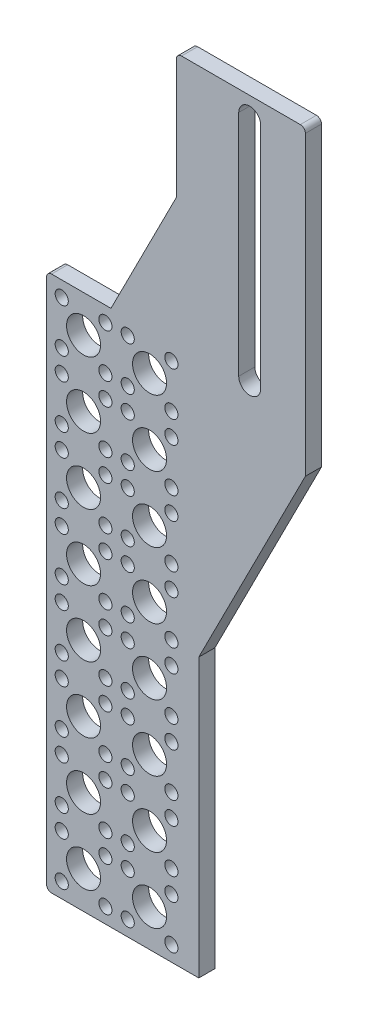
SolidWorks part; units mm, degrees
ref_plane "Front Plane" through (0, 0, 0) normal (0, 0, 1) x (1, 0, 0)
ref_plane "Top Plane" through (0, 0, 0) normal (0, 1, 0) x (1, 0, 0)
ref_plane "Right Plane" through (0, 0, 0) normal (1, 0, 0) x (0, 0, -1)
sketch "Reference Sketch" plane through (0, 0, 0) normal (0, 0, 1) x (1, 0, 0)
  line L0 (0, 0) -> (0, 25.019) construction
  line L1 (35.019, 0) -> (35.019, -50.019) construction
  line L2 (-1.725, 25.019) -> (1.725, 25.019)
  line L6 (35.019, -50.019) -> (-35.019, -50.019) construction
  line L7 (-35.019, 0) -> (-112.4213, 0) construction
  line L8 (-35.019, -50.019) -> (-35.019, 0) construction
  line L9 (0, -35.019) -> (0, -50.019) construction
  line L10 (-35.019, -50.019) -> (-75, -50.019)
  line L11 (35.019, 0) -> (112.4213, 0) construction
  line L12 (-75, -50.019) -> (-75, -120.019)
  line L13 (-75, -120.019) -> (75, -120.019)
  line L14 (75, -120.019) -> (75, -50.019)
  line L15 (35.019, -50.019) -> (75, -50.019)
  line L16 (0, 35.019) -> (70, 35.019)
  line L17 (70, 35.019) -> (70, -35.019)
  line L19 (0, 35.019) -> (-70, 35.019)
  line L20 (-70, 35.019) -> (-70, -35.019)
  line L22 (-35, -35.019) -> (-35.019, -50.019)
  line L23 (-128.24, -30) -> (-108.24, -30) construction
  line L24 (-128.24, -30) -> (-128.24, -140) construction
  line L25 (-128.24, -140) -> (-108.24, -140) construction
  line L26 (-108.24, -30) -> (-108.24, -140) construction
  line L27 (35.019, -50.019) -> (35, -35.019)
  line L28 (70, -35.019) -> (35, -35.019)
  line L29 (-50, -55.019) -> (50, -55.019) construction
  line L30 (-50, -55.019) -> (-50, -115.019) construction
  line L31 (-50, -115.019) -> (50, -115.019) construction
  line L32 (50, -55.019) -> (50, -115.019) construction
  line L33 (-35, -35.019) -> (-70, -35.019)
  circle A0 centre (0, 0) radius 25.019 construction
  circle A1 centre (0, 25.019) radius 1.725 construction
  circle A2 centre (17.6911, 17.6911) radius 1.725 construction
  circle A3 centre (25.019, 0) radius 1.725 construction
  circle A4 centre (17.6911, -17.6911) radius 1.725 construction
  circle A5 centre (0, -25.019) radius 1.725 construction
  circle A6 centre (-17.6911, -17.6911) radius 1.725 construction
  circle A7 centre (0, -82.931) radius 139.7 construction
  circle A8 centre (0, -82.931) radius 13.9065 construction
  circle A9 centre (0, 0) radius 35.019 construction
  circle A10 centre (-25.019, 0) radius 1.725 construction
  circle A11 centre (-17.6911, 17.6911) radius 1.725 construction
  circle A12 centre (0, 0) radius 2.16 construction
  circle A13 centre (-63.2127, 5.019) radius 2.16
  circle A14 centre (-63.2127, 5.019) radius 2.8702 construction
  circle A15 centre (-53.2127, 5.019) radius 2.16
  circle A16 centre (-53.2127, 5.019) radius 2.8702 construction
  circle A17 centre (-53.2127, -4.981) radius 2.16
  circle A18 centre (-53.2127, -4.981) radius 2.8702 construction
  circle A19 centre (-53.2127, -14.981) radius 2.16
  circle A20 centre (-53.2127, -14.981) radius 2.8702 construction
  circle A21 centre (-53.2127, -24.981) radius 2.16
  circle A22 centre (-53.2127, -24.981) radius 2.8702 construction
  circle A23 centre (-63.2127, -4.981) radius 2.16
  circle A24 centre (-63.2127, -4.981) radius 2.8702 construction
  circle A25 centre (-63.2127, -14.981) radius 2.16
  circle A26 centre (-63.2127, -14.981) radius 2.8702 construction
  circle A27 centre (-63.2127, -24.981) radius 2.16
  circle A28 centre (-63.2127, -24.981) radius 2.8702 construction
  circle A29 centre (0, -82.931) radius 177.8 construction
  point P23 (0, 56.769)
  point P52 (0, -115.019)
  point P54 (50, -85.019)
  point P56 (75, -85.019)
  point P63 (35.0095, -42.519)
  point P64 (0, -42.519)
  dimension "D1" = 50.038
  dimension "D2" = 3.45
  dimension "D5" = 279.4
  dimension "D10" = 27.813
  dimension "D12" = 10
  dimension "D19" = 4.32
  dimension "D21" = 70.038
  dimension "D22" = 50.038
  dimension "D23" = 4.32
  dimension "D24" = 5.7404
  dimension "D31" = 355.6
  dimension "D4" = 25.019
  dimension "D6" = 31.75
  dimension "D7" = 15
  dimension "D8" = 70
  dimension "D9" = 108.24
  dimension "D11" = 30
  dimension "D13" = 20
  dimension "D14" = 110
  dimension "D15" = 150
  dimension "D16" = 70
  dimension "D17" = 100
  dimension "D18" = 60
  dimension "D20" = 35
  dimension "D27" = 10
  dimension "D28" = 10
  dimension "D29" = 30
  dimension "D30" = 6.7873
  dimension "D25" = 2
  dimension "D26" = 4
  dimension "D3" = 8
sketch "Sketch2" plane through (0, 0, 0) normal (0, 0, 1) x (1, 0, 0)
  line L0 (-116.64, -33.131) -> (-125.24, -33.131) construction
  line L2 (-128.24, -30.131) -> (-128.24, -135.731)
  line L3 (-128.24, -135.731) -> (-98.24, -135.731)
  line L5 (-125.24, -33.131) -> (-125.24, -41.731) construction
  line L6 (-77.24, -30.131) -> (-77.24, -39.631)
  line L8 (-102.64, -30.131) -> (-102.64, 19.869)
  line L9 (-102.64, 19.869) -> (-77.24, 19.869)
  line L10 (-77.24, -30.131) -> (-77.24, 19.869)
  line L11 (-88.2127, 15.869) -> (-88.2127, -29.131) construction
  line L12 (-86.0527, 15.869) -> (-86.0527, -29.131)
  line L13 (-90.3727, 15.869) -> (-90.3727, -29.131)
  line L14 (-128.24, -30.131) -> (-77.24, -30.131)
  line L15 (0, -82.931) -> (139.7, -82.931) construction
  line L16 (-128.24, -30) -> (-128.24, -140) construction
  line L17 (-102.64, -4.731) -> (-115.54, -30.131)
  line L20 (-77.24, -39.631) -> (-98.24, -80.9798)
  line L21 (-77.24, -39.631) -> (-128.24, -39.631) construction
  line L22 (-98.24, -80.9798) -> (-98.24, -135.731)
  line L23 (-101.59, -43.781) -> (-101.59, -31.081) construction
  line L24 (-114.59, -43.781) -> (-127.29, -43.781) construction
  line L25 (-114.59, -43.781) -> (-114.59, -31.081) construction
  line L26 (-114.59, -31.081) -> (-127.29, -31.081) construction
  line L27 (-127.29, -43.781) -> (-127.29, -31.081) construction
  line L28 (-101.59, -43.781) -> (-114.29, -43.781) construction
  line L29 (-101.59, -31.081) -> (-114.29, -31.081) construction
  line L30 (-114.29, -43.781) -> (-114.29, -31.081) construction
  line L31 (-101.59, -56.781) -> (-101.59, -44.081) construction
  line L32 (-101.59, -56.781) -> (-114.29, -56.781) construction
  line L33 (-101.59, -44.081) -> (-114.29, -44.081) construction
  line L34 (-114.29, -56.781) -> (-114.29, -44.081) construction
  line L35 (-101.59, -69.781) -> (-101.59, -57.081) construction
  line L36 (-101.59, -69.781) -> (-114.29, -69.781) construction
  line L37 (-101.59, -57.081) -> (-114.29, -57.081) construction
  line L38 (-114.29, -69.781) -> (-114.29, -57.081) construction
  line L39 (-101.59, -82.781) -> (-101.59, -70.081) construction
  line L40 (-101.59, -82.781) -> (-114.29, -82.781) construction
  line L41 (-101.59, -70.081) -> (-114.29, -70.081) construction
  line L42 (-114.29, -82.781) -> (-114.29, -70.081) construction
  line L43 (-101.59, -95.781) -> (-101.59, -83.081) construction
  line L44 (-101.59, -95.781) -> (-114.29, -95.781) construction
  line L45 (-101.59, -83.081) -> (-114.29, -83.081) construction
  line L46 (-114.29, -95.781) -> (-114.29, -83.081) construction
  line L47 (-101.59, -108.781) -> (-101.59, -96.081) construction
  line L48 (-101.59, -108.781) -> (-114.29, -108.781) construction
  line L49 (-101.59, -96.081) -> (-114.29, -96.081) construction
  line L50 (-114.29, -108.781) -> (-114.29, -96.081) construction
  line L51 (-101.59, -121.781) -> (-101.59, -109.081) construction
  line L52 (-101.59, -121.781) -> (-114.29, -121.781) construction
  line L53 (-101.59, -109.081) -> (-114.29, -109.081) construction
  line L54 (-114.29, -121.781) -> (-114.29, -109.081) construction
  line L55 (-101.59, -134.781) -> (-101.59, -122.081) construction
  line L56 (-101.59, -134.781) -> (-114.29, -134.781) construction
  line L57 (-101.59, -122.081) -> (-114.29, -122.081) construction
  line L58 (-114.29, -134.781) -> (-114.29, -122.081) construction
  line L59 (-114.59, -56.781) -> (-114.59, -44.081) construction
  line L60 (-114.59, -56.781) -> (-127.29, -56.781) construction
  line L61 (-114.59, -44.081) -> (-127.29, -44.081) construction
  line L62 (-127.29, -56.781) -> (-127.29, -44.081) construction
  line L63 (-114.59, -69.781) -> (-114.59, -57.081) construction
  line L64 (-114.59, -69.781) -> (-127.29, -69.781) construction
  line L65 (-114.59, -57.081) -> (-127.29, -57.081) construction
  line L66 (-127.29, -69.781) -> (-127.29, -57.081) construction
  line L67 (-114.59, -82.781) -> (-114.59, -70.081) construction
  line L68 (-114.59, -82.781) -> (-127.29, -82.781) construction
  line L69 (-114.59, -70.081) -> (-127.29, -70.081) construction
  line L70 (-127.29, -82.781) -> (-127.29, -70.081) construction
  line L71 (-114.59, -95.781) -> (-114.59, -83.081) construction
  line L72 (-114.59, -95.781) -> (-127.29, -95.781) construction
  line L73 (-114.59, -83.081) -> (-127.29, -83.081) construction
  line L74 (-127.29, -95.781) -> (-127.29, -83.081) construction
  line L75 (-114.59, -108.781) -> (-114.59, -96.081) construction
  line L76 (-114.59, -108.781) -> (-127.29, -108.781) construction
  line L77 (-114.59, -96.081) -> (-127.29, -96.081) construction
  line L78 (-127.29, -108.781) -> (-127.29, -96.081) construction
  line L79 (-114.59, -121.781) -> (-114.59, -109.081) construction
  line L80 (-114.59, -121.781) -> (-127.29, -121.781) construction
  line L81 (-114.59, -109.081) -> (-127.29, -109.081) construction
  line L82 (-127.29, -121.781) -> (-127.29, -109.081) construction
  line L83 (-114.59, -134.781) -> (-114.59, -122.081) construction
  line L84 (-114.59, -134.781) -> (-127.29, -134.781) construction
  line L85 (-114.59, -122.081) -> (-127.29, -122.081) construction
  line L86 (-127.29, -134.781) -> (-127.29, -122.081) construction
  circle A0 centre (-125.24, -33.131) radius 1.2954
  circle A1 centre (-125.24, -41.731) radius 1.2954
  circle A2 centre (-120.94, -37.431) radius 3.35
  circle A3 centre (-116.64, -33.131) radius 1.2954
  circle A4 centre (-116.64, -41.731) radius 1.2954
  arc A80 (-86.0527, 15.869) -> (-90.3727, 15.869) centre (-88.2127, 15.869) ccw
  arc A81 (-90.3727, -29.131) -> (-86.0527, -29.131) centre (-88.2127, -29.131) ccw
  circle A82 centre (0, -82.931) radius 139.7 construction
  circle A83 centre (-107.94, -37.431) radius 3.35
  circle A84 centre (-103.64, -33.131) radius 1.2954
  circle A85 centre (-112.24, -41.731) radius 1.2954
  circle A86 centre (-112.24, -33.131) radius 1.2954
  circle A87 centre (-103.64, -41.731) radius 1.2954
  circle A88 centre (-107.94, -50.431) radius 3.35
  circle A89 centre (-103.64, -46.131) radius 1.2954
  circle A90 centre (-112.24, -54.731) radius 1.2954
  circle A91 centre (-112.24, -46.131) radius 1.2954
  circle A92 centre (-103.64, -54.731) radius 1.2954
  circle A93 centre (-107.94, -63.431) radius 3.35
  circle A94 centre (-103.64, -59.131) radius 1.2954
  circle A95 centre (-112.24, -67.731) radius 1.2954
  circle A96 centre (-112.24, -59.131) radius 1.2954
  circle A97 centre (-103.64, -67.731) radius 1.2954
  circle A98 centre (-107.94, -76.431) radius 3.35
  circle A99 centre (-103.64, -72.131) radius 1.2954
  circle A100 centre (-112.24, -80.731) radius 1.2954
  circle A101 centre (-112.24, -72.131) radius 1.2954
  circle A102 centre (-103.64, -80.731) radius 1.2954
  circle A103 centre (-107.94, -89.431) radius 3.35
  circle A104 centre (-103.64, -85.131) radius 1.2954
  circle A105 centre (-112.24, -93.731) radius 1.2954
  circle A106 centre (-112.24, -85.131) radius 1.2954
  circle A107 centre (-103.64, -93.731) radius 1.2954
  circle A108 centre (-107.94, -102.431) radius 3.35
  circle A109 centre (-103.64, -98.131) radius 1.2954
  circle A110 centre (-112.24, -106.731) radius 1.2954
  circle A111 centre (-112.24, -98.131) radius 1.2954
  circle A112 centre (-103.64, -106.731) radius 1.2954
  circle A113 centre (-107.94, -115.431) radius 3.35
  circle A114 centre (-103.64, -111.131) radius 1.2954
  circle A115 centre (-112.24, -119.731) radius 1.2954
  circle A116 centre (-112.24, -111.131) radius 1.2954
  circle A117 centre (-103.64, -119.731) radius 1.2954
  circle A118 centre (-107.94, -128.431) radius 3.35
  circle A119 centre (-103.64, -124.131) radius 1.2954
  circle A120 centre (-112.24, -132.731) radius 1.2954
  circle A121 centre (-112.24, -124.131) radius 1.2954
  circle A122 centre (-103.64, -132.731) radius 1.2954
  circle A123 centre (-120.94, -50.431) radius 3.35
  circle A124 centre (-116.64, -46.131) radius 1.2954
  circle A125 centre (-125.24, -54.731) radius 1.2954
  circle A126 centre (-125.24, -46.131) radius 1.2954
  circle A127 centre (-116.64, -54.731) radius 1.2954
  circle A128 centre (-120.94, -63.431) radius 3.35
  circle A129 centre (-116.64, -59.131) radius 1.2954
  circle A130 centre (-125.24, -67.731) radius 1.2954
  circle A131 centre (-125.24, -59.131) radius 1.2954
  circle A132 centre (-116.64, -67.731) radius 1.2954
  circle A133 centre (-120.94, -76.431) radius 3.35
  circle A134 centre (-116.64, -72.131) radius 1.2954
  circle A135 centre (-125.24, -80.731) radius 1.2954
  circle A136 centre (-125.24, -72.131) radius 1.2954
  circle A137 centre (-116.64, -80.731) radius 1.2954
  circle A138 centre (-120.94, -89.431) radius 3.35
  circle A139 centre (-116.64, -85.131) radius 1.2954
  circle A140 centre (-125.24, -93.731) radius 1.2954
  circle A141 centre (-125.24, -85.131) radius 1.2954
  circle A142 centre (-116.64, -93.731) radius 1.2954
  circle A143 centre (-120.94, -102.431) radius 3.35
  circle A144 centre (-116.64, -98.131) radius 1.2954
  circle A145 centre (-125.24, -106.731) radius 1.2954
  circle A146 centre (-125.24, -98.131) radius 1.2954
  circle A147 centre (-116.64, -106.731) radius 1.2954
  circle A148 centre (-120.94, -115.431) radius 3.35
  circle A149 centre (-116.64, -111.131) radius 1.2954
  circle A150 centre (-125.24, -119.731) radius 1.2954
  circle A151 centre (-125.24, -111.131) radius 1.2954
  circle A152 centre (-116.64, -119.731) radius 1.2954
  circle A153 centre (-120.94, -128.431) radius 3.35
  circle A154 centre (-116.64, -124.131) radius 1.2954
  circle A155 centre (-125.24, -132.731) radius 1.2954
  circle A156 centre (-125.24, -124.131) radius 1.2954
  circle A157 centre (-116.64, -132.731) radius 1.2954
  point P14 (-120.94, -33.131)
  point P15 (-125.24, -37.431)
  point P17 (-88.2127, -6.631)
  point P21 (-120.94, -31.081)
  point P22 (-114.59, -37.431)
  point P23 (0, 0)
  point P24 (-128.19, -142.6712)
  point P195 (-128.24, -82.931)
  dimension "D1" = 2.5908
  dimension "D3" = 6.7
  dimension "D10" = 2.16
  dimension "D2" = 8.6
  dimension "D5" = 3
  dimension "D12" = 50
  dimension "D13" = 25.4
  dimension "D11" = 3
  dimension "D14" = 4
  dimension "D15" = 45
  dimension "D17" = 12.7
  dimension "D18" = 25.4
  dimension "D21" = 30
  dimension "D9" = 9.5
  dimension "D19" = 21
  dimension "D4" = 25
  dimension "D7" = 12.7
  dimension "D8" = 13
  dimension "D16" = 13
  dimension "D22" = 3
  dimension "D6" = 2
  dimension "D20" = 8
extrude "Boss-Extrude1" add sketch "Sketch2" along normal blind 3.175
fillet "Fillet1" radius 1 1 edges at (-102.64, 19.869, 1.5875)
fillet "Fillet2" radius 1 3 edges at (-128.24, -135.731, 1.5875) (-128.24, -30.131, 1.5875) (-77.24, 19.869, 1.5875)
equation "\"D22@Sketch2\"=\"D11@Sketch2\""
equation "\"D5@Sketch2\"=\"D11@Sketch2\""
